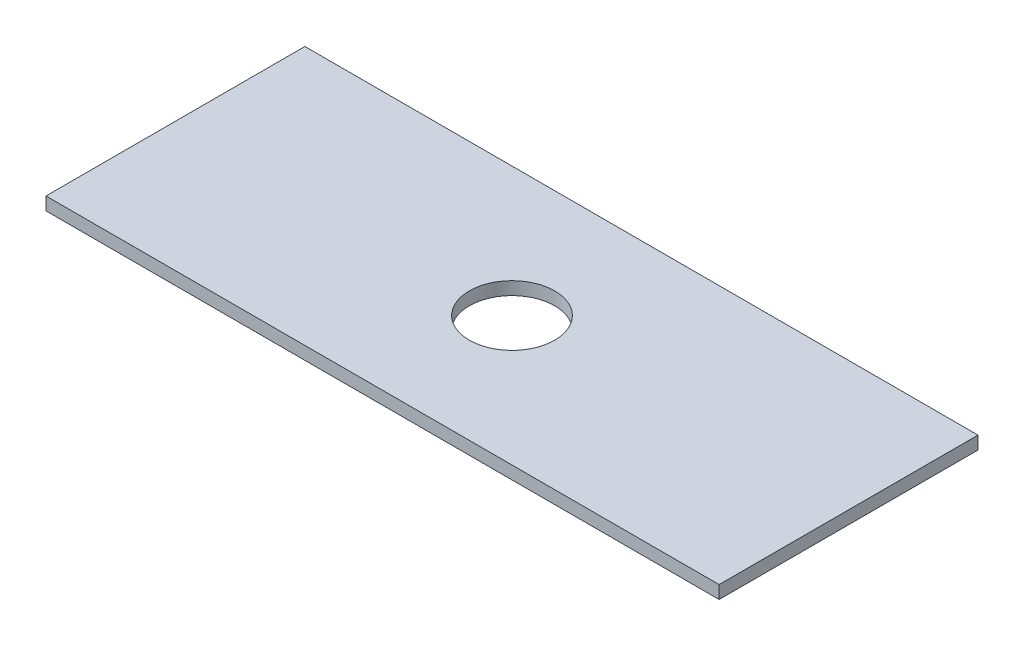
SolidWorks part; units mm, degrees
ref_plane "Front Plane" through (0, 0, 0) normal (0, 0, 1) x (1, 0, 0)
ref_plane "Top Plane" through (0, 0, 0) normal (0, 1, 0) x (1, 0, 0)
ref_plane "Right Plane" through (0, 0, 0) normal (1, 0, 0) x (0, 0, -1)
sketch "Sketch1" plane through (0, 0, 0) normal (0, 1, 0) x (1, 0, 0)
  line L0 (0, 50) -> (130, 0) construction
  line L1 (0, 0) -> (130, 0)
  line L2 (0, 0) -> (0, 50)
  line L3 (0, 50) -> (130, 50)
  line L4 (130, 0) -> (130, 50)
  line L5 (130, 50) -> (0, 0) construction
  circle A0 centre (65, 25) radius 8.25
  point P7 (65, 25)
  dimension "D3" = 16.5
  dimension "D1" = 50
  dimension "D2" = 130
extrude "Boss-Extrude1" add sketch "Sketch1" along normal blind 2.5
